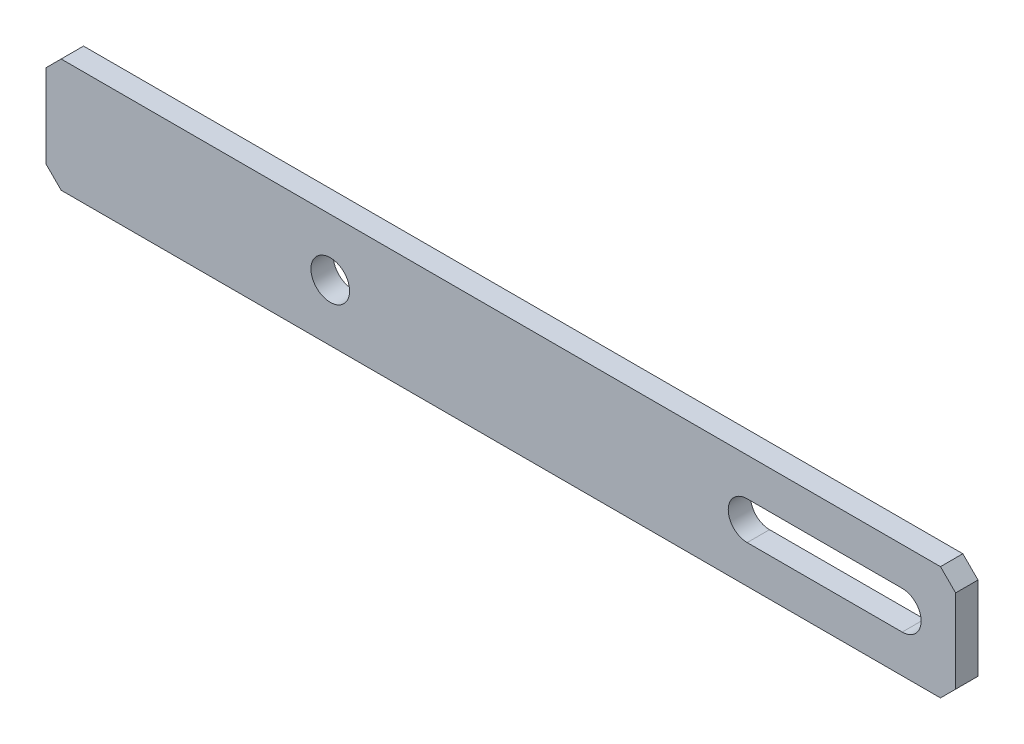
SolidWorks part; units mm, degrees
ref_plane "Front Plane" through (0, 0, 0) normal (0, 0, 1) x (1, 0, 0)
ref_plane "Top Plane" through (0, 0, 0) normal (0, 1, 0) x (1, 0, 0)
ref_plane "Right Plane" through (0, 0, 0) normal (1, 0, 0) x (0, 0, -1)
sketch "Sketch1" plane through (0, 0, 0) normal (0, 0, 1) x (1, 0, 0)
  line L0 (0.3801, 31.6809) -> (20.8301, 31.6809)
  line L1 (-92.1199, 36.6809) -> (27.8801, 36.6809)
  line L2 (-92.1199, 36.6809) -> (-92.1199, 21.6809)
  line L3 (-92.1199, 21.6809) -> (27.8801, 21.6809)
  line L4 (27.8801, 36.6809) -> (27.8801, 21.6809)
  line L5 (-92.1199, 36.6809) -> (27.8801, 21.6809) construction
  line L6 (-92.1199, 21.6809) -> (27.8801, 36.6809) construction
  line L7 (0.3801, 26.6809) -> (20.8301, 26.6809)
  circle A0 centre (-54.6199, 29.1809) radius 2.55
  arc A1 (0.3801, 31.6809) -> (0.3801, 26.6809) centre (0.3801, 29.1809) ccw
  arc A2 (20.8301, 26.6809) -> (20.8301, 31.6809) centre (20.8301, 29.1809) ccw
  point P0 (-32.1199, 29.1809)
  dimension "D3" = 37.5
  dimension "D6" = 5.1
  dimension "D7" = 5
  dimension "D8" = 5
  dimension "D1" = 120
  dimension "D2" = 15
  dimension "D4" = 92.5
  dimension "D5" = 112.95
extrude "Boss-Extrude1" add sketch "Sketch1" along normal blind 2.95
chamfer "Chamfer1" distance 2 angle 45 4 edges at (27.8801, 36.6809, 1.475) (27.8801, 21.6809, 1.475) (-92.1199, 21.6809, 1.475) (-92.1199, 36.6809, 1.475)
